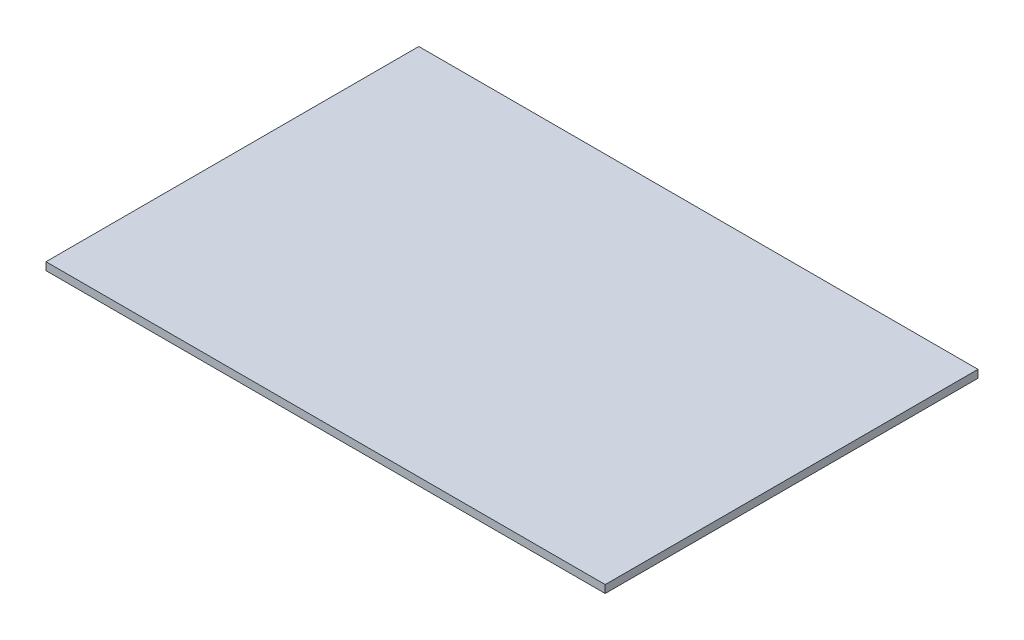
SolidWorks part; units mm, degrees
ref_plane "Front" through (0, 0, 0) normal (0, 0, 1) x (1, 0, 0)
ref_plane "Top" through (0, 0, 0) normal (0, 1, 0) x (1, 0, 0)
ref_plane "Right" through (0, 0, 0) normal (1, 0, 0) x (0, 0, -1)
sketch "Box Top Sketch" plane through (0, 0, 0) normal (0, 1, 0) x (1, 0, 0)
  line L1 (0, 0) -> (228.6, 0)
  line L2 (0, 0) -> (0, 152.4)
  line L3 (0, 152.4) -> (228.6, 152.4)
  line L4 (228.6, 0) -> (228.6, 152.4)
  point P5 (0, 50.8)
  dimension "D1" = 228.6
  dimension "D2" = 152.4
extrude "Boss-Extrude1" add sketch "Box Top Sketch" along normal blind 3.175
sketch "Passthrough Hole Sketch" plane through (0, 3.175, 0) normal (0, 1, 0) x (1, 0, 0)
  line L0 (34.544, 152.4) -> (34.544, 0) construction
  line L1 (228.6, 152.4) -> (0, 152.4) construction
  line L2 (0, 0) -> (228.6, 0) construction
  line L3 (0, 152.4) -> (0, 0) construction
  line L4 (39.624, 152.4) -> (39.624, 0) construction
  line L5 (108.204, 152.4) -> (108.204, 0) construction
  circle A0 centre (108.204, 76.2) radius 68.58
  circle A1 centre (108.204, 76.2) radius 73.66
  dimension "D1" = 34.544
  dimension "D2" = 5.08
  dimension "D3" = 68.58
